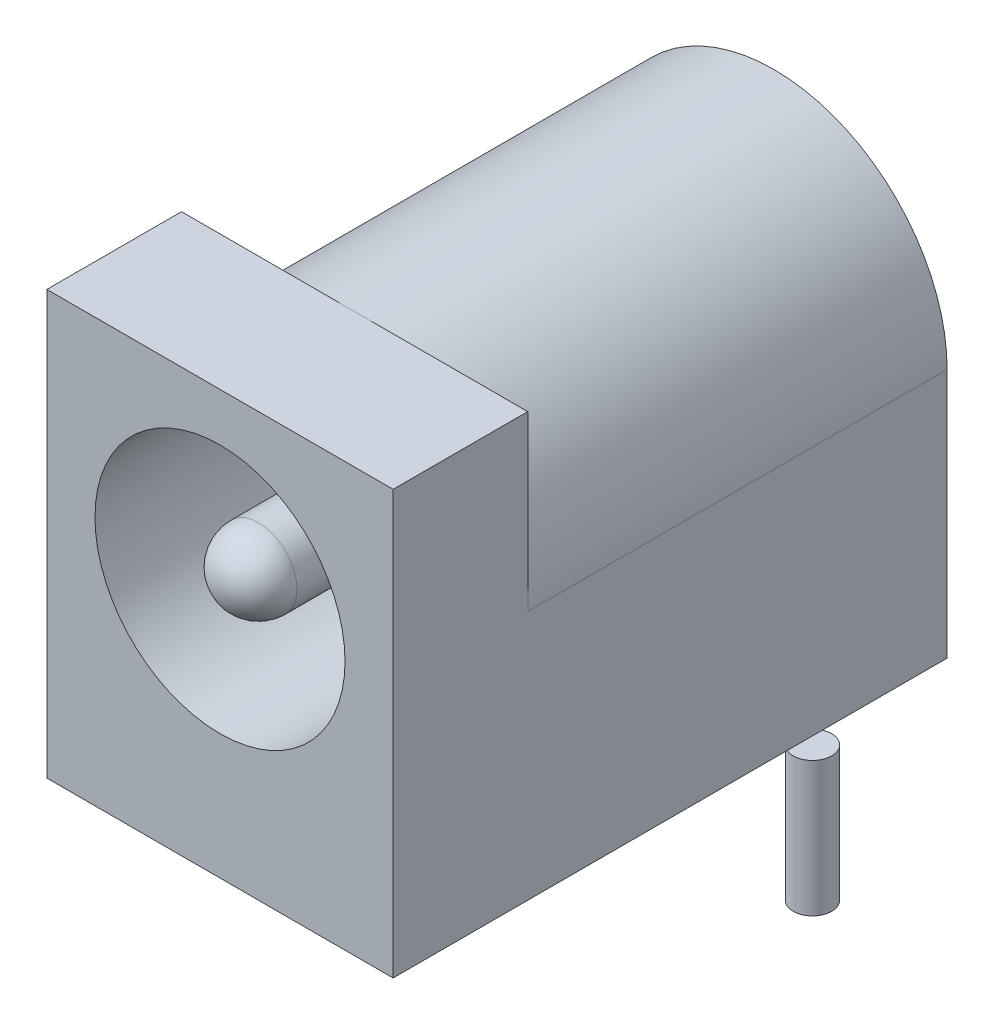
SolidWorks part; units mm, degrees
material "ABS"
ref_plane "Front Plane" through (0, 0, 0) normal (0, 0, 1) x (1, 0, 0)
ref_plane "Top Plane" through (0, 0, 0) normal (0, 1, 0) x (1, 0, 0)
ref_plane "Right Plane" through (0, 0, 0) normal (1, 0, 0) x (0, 0, -1)
sketch "Sketch1" plane through (0, 0, 0) normal (0, 0, 1) x (1, 0, 0)
  line L0 (4.5, 0) -> (-4.5, 0)
  line L1 (-4.5, 0) -> (-4.5, 6.5)
  line L2 (4.5, 6.5) -> (4.5, 0)
  line L3 (4.5, 6.5) -> (-4.5, 6.5) construction
  arc A0 (-4.5, 6.5) -> (4.5, 6.5) centre (0, 6.5) cw
  point P4 (0, 0)
  point P9 (4.5, 0)
  dimension "D1" = 9
  dimension "D2" = 6.5
extrude "Boss-Extrude1" add sketch "Sketch1" against normal blind 14.4
sketch "Sketch3" plane through (0, 0, 0) normal (0, 0, 1) x (1, 0, 0)
  line L1 (-4.5, 6.5) -> (4.5, 6.5)
  line L2 (-4.5, 6.5) -> (-4.5, 11)
  line L3 (-4.5, 11) -> (4.5, 11)
  line L4 (4.5, 6.5) -> (4.5, 11)
  arc A0 (4.5, 6.5) -> (-4.5, 6.5) centre (0, 6.5) ccw construction
  point P5 (4.5, 6.5)
extrude "Boss-Extrude2" add sketch "Sketch3" against normal blind 3.5
sketch "Sketch2" plane through (0, 0, 0) normal (0, 0, 1) x (1, 0, 0)
  circle A0 centre (0, 6.5) radius 3.25
  circle A1 centre (0, 6.5) radius 1
  dimension "D1" = 6.5
  dimension "D2" = 2
extrude "Cut-Extrude1" cut sketch "Sketch2" against normal blind 10
fillet "Fillet1" radius 1 1 edges at (1, 6.5, 0)
sketch "Sketch4" plane through (0, 0, 0) normal (0, -1, 0) x (1, 0, 0)
  line L0 (0, 0) -> (0, -14.4) construction
  line L1 (-4.5, 0) -> (4.5, 0) construction
  line L2 (-4.5, -14.4) -> (4.5, -14.4) construction
  line L4 (0, -7.7) -> (0, -13.7) construction
  line L5 (0, -10.7) -> (4.7, -10.7) construction
  circle A0 centre (0, -13.7) radius 0.5
  circle A1 centre (0, -7.7) radius 0.5
  circle A2 centre (4.7, -10.7) radius 0.5
  point P12 (5.7848, -10.782)
  point P13 (0, -7.1668)
  point P15 (0, 0)
  point P16 (0, 0)
  dimension "D1" = 1
  dimension "D2" = 6
  dimension "D3" = 4.7
  dimension "D4" = 10.7
extrude "Boss-Extrude3" add sketch "Sketch4" along normal blind 3.5
